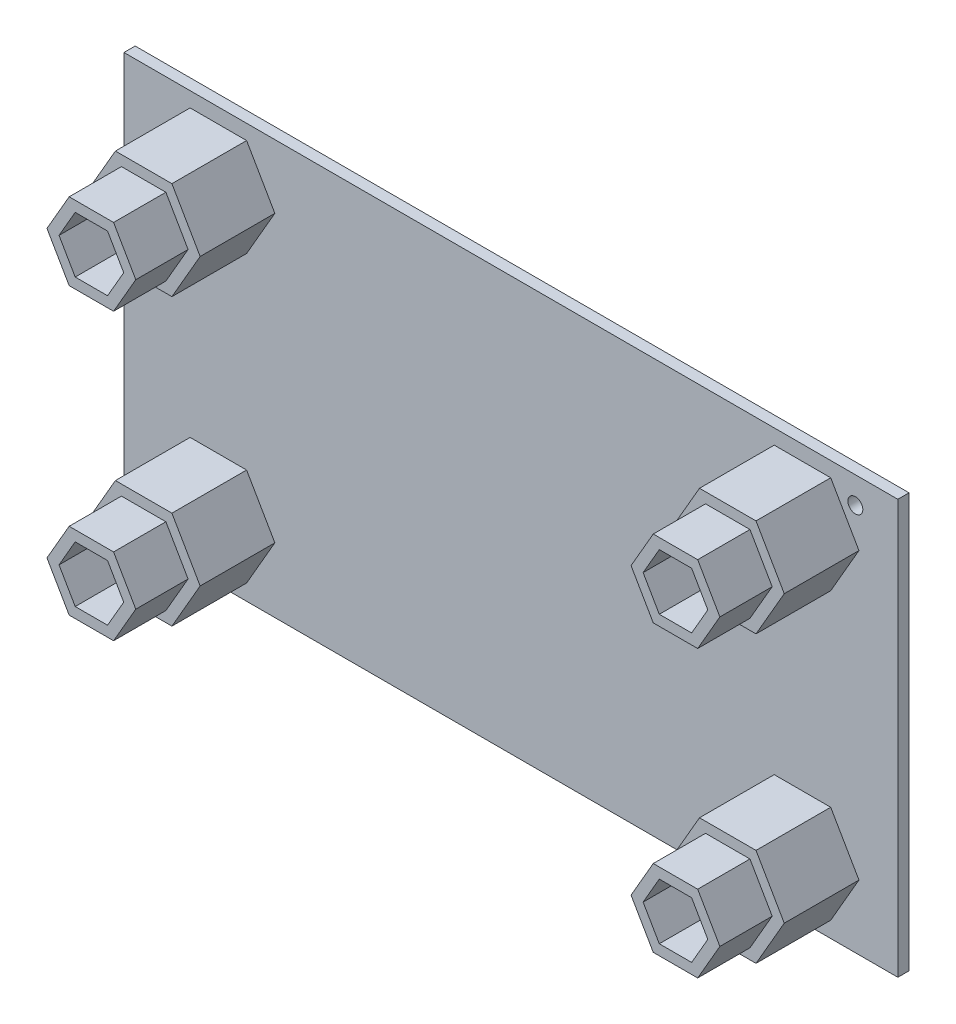
SolidWorks part; units mm, degrees
ref_plane "Front Plane" through (0, 0, 0) normal (0, 0, 1) x (1, 0, 0)
ref_plane "Top Plane" through (0, 0, 0) normal (0, 1, 0) x (1, 0, 0)
ref_plane "Right Plane" through (0, 0, 0) normal (1, 0, 0) x (0, 0, -1)
sketch "Sketch1" plane through (0, 0, 0) normal (0, 0, 1) x (1, 0, 0)
  line L1 (0, 0) -> (103.6, 0)
  line L2 (0, 0) -> (0, 55.42)
  line L3 (0, 55.42) -> (103.6, 55.42)
  line L4 (103.6, 0) -> (103.6, 55.42)
  dimension "D1" = 103.6
  dimension "D2" = 55.42
extrude "Boss-Extrude1" add sketch "Sketch1" along normal blind 1.5
sketch "Sketch2" plane through (0, 0, 0) normal (0, 0, -1) x (-1, 0, 0)
  line L0 (-103.6, 3.54) -> (0, 3.54) construction
  line L1 (-103.6, 0) -> (-103.6, 55.42) construction
  line L2 (0, 55.42) -> (0, 0) construction
  line L3 (0, 0) -> (-103.6, 0) construction
  line L4 (-103.6, 51.88) -> (0, 51.88) construction
  line L5 (-55.3364, 55.42) -> (-55.3364, 51.88) construction
  line L6 (-103.6, 55.42) -> (0, 55.42) construction
  line L7 (-47.0331, 0) -> (-47.0331, 3.54) construction
  circle A0 centre (-90.42, 3.54) radius 1
  circle A1 centre (-15.28, 3.54) radius 1
  circle A2 centre (-97.91, 51.88) radius 1
  circle A3 centre (-15.28, 51.88) radius 1
  dimension "D3" = 2
  dimension "D1" = 3.54
  dimension "D2" = 5.69
  dimension "D4" = 75.14
  dimension "D5" = 7.49
extrude "Cut-Extrude1" cut sketch "Sketch2" against normal blind 1.5
sketch "Sketch3" plane through (0, 0, 1.5) normal (0, 0, 1) x (1, 0, 0)
  line L0 (0, 52.02) -> (103.6, 52.02) construction
  line L1 (0, 55.42) -> (0, 0) construction
  line L2 (103.6, 0) -> (103.6, 55.42) construction
  line L3 (28.7266, 55.42) -> (28.7266, 52.02) construction
  line L4 (103.6, 55.42) -> (0, 55.42) construction
  line L5 (0, 27.77) -> (103.6, 27.77) construction
  line L6 (9.6634, 41.72) -> (15.6101, 41.72)
  line L7 (15.6101, 41.72) -> (18.5834, 46.87)
  line L8 (18.5834, 46.87) -> (15.6101, 52.02)
  line L9 (15.6101, 52.02) -> (9.6634, 52.02)
  line L10 (9.6634, 52.02) -> (6.69, 46.87)
  line L11 (6.69, 46.87) -> (9.6634, 41.72)
  line L12 (6.69, 8.67) -> (9.6634, 13.82)
  line L13 (9.6634, 3.52) -> (6.69, 8.67)
  line L14 (15.6101, 3.52) -> (9.6634, 3.52)
  line L15 (18.5834, 8.67) -> (15.6101, 3.52)
  line L16 (15.6101, 13.82) -> (18.5834, 8.67)
  line L17 (9.6634, 13.82) -> (15.6101, 13.82)
  line L18 (51.7334, -0.2211) -> (51.7334, 55.1859) construction
  line L20 (96.7768, 46.87) -> (93.8035, 41.72)
  line L21 (93.8035, 52.02) -> (96.7768, 46.87)
  line L22 (87.8568, 52.02) -> (93.8035, 52.02)
  line L23 (84.8834, 46.87) -> (87.8568, 52.02)
  line L24 (87.8568, 41.72) -> (84.8834, 46.87)
  line L25 (93.8035, 41.72) -> (87.8568, 41.72)
  line L26 (93.8035, 13.82) -> (87.8568, 13.82)
  line L27 (87.8568, 13.82) -> (84.8834, 8.67)
  line L28 (84.8834, 8.67) -> (87.8568, 3.52)
  line L29 (87.8568, 3.52) -> (93.8035, 3.52)
  line L30 (93.8035, 3.52) -> (96.7768, 8.67)
  line L31 (96.7768, 8.67) -> (93.8035, 13.82)
  circle A0 centre (12.6367, 46.87) radius 5.15 construction
  circle A1 centre (12.6367, 8.67) radius 5.15 construction
  circle A2 centre (90.8301, 46.87) radius 5.15 construction
  circle A3 centre (90.8301, 8.67) radius 5.15 construction
  dimension "D1" = 3.4
  dimension "D2" = 10.3
  dimension "D3" = 6.69
  dimension "D4" = 66.3
  dimension "D5" = 38.2
extrude "Boss-Extrude2" add sketch "Sketch3" along normal blind 17
sketch "Sketch4" plane through (0, 0, 1.5) normal (0, 0, 1) x (1, 0, 0)
  line L4 (18.5834, 46.87) -> (16.0554, 51.2486) construction
  line L5 (15.6101, 41.72) -> (18.5834, 46.87) construction
  line L6 (16.0554, 51.2486) -> (15.6101, 52.02) construction
  line L7 (15.6101, 52.02) -> (14.2898, 52.02) construction
  line L36 (14.2898, 52.02) -> (9.6634, 52.02) construction
  line L37 (9.6634, 52.02) -> (6.69, 46.87) construction
  line L38 (6.69, 46.87) -> (9.6634, 41.72) construction
  line L39 (9.6634, 41.72) -> (15.6101, 41.72) construction
  line L40 (9.6634, 3.52) -> (14.2802, 3.52) construction
  line L41 (15.6101, 3.52) -> (16.0138, 4.2193) construction
  line L42 (16.0138, 4.2193) -> (18.5834, 8.67) construction
  line L43 (14.2802, 3.52) -> (15.6101, 3.52) construction
  line L44 (18.5834, 8.67) -> (15.6101, 13.82) construction
  line L45 (15.6101, 13.82) -> (9.6634, 13.82) construction
  line L46 (9.6634, 13.82) -> (6.69, 8.67) construction
  line L47 (6.69, 8.67) -> (9.6634, 3.52) construction
  line L48 (84.8834, 8.67) -> (87.8568, 3.52) construction
  line L49 (87.8568, 13.82) -> (84.8834, 8.67) construction
  line L50 (91.4198, 3.52) -> (93.8035, 3.52) construction
  line L51 (89.4202, 3.52) -> (91.4198, 3.52) construction
  line L52 (87.8568, 3.52) -> (89.4202, 3.52) construction
  line L53 (93.8035, 3.52) -> (96.7768, 8.67) construction
  line L54 (96.7768, 8.67) -> (93.8035, 13.82) construction
  line L55 (93.8035, 13.82) -> (87.8568, 13.82) construction
  line L58 (96.7768, 46.87) -> (93.8035, 52.02) construction
  line L59 (93.8035, 52.02) -> (87.8568, 52.02) construction
  line L60 (93.8035, 41.72) -> (96.7768, 46.87) construction
  line L61 (87.8568, 41.72) -> (93.8035, 41.72) construction
  line L62 (84.8834, 46.87) -> (87.8568, 41.72) construction
  line L63 (87.8568, 52.02) -> (84.8834, 46.87) construction
  line L64 (18.5834, 46.87) -> (16.0554, 51.2486)
  line L65 (15.6101, 41.72) -> (18.5834, 46.87)
  line L66 (16.0554, 51.2486) -> (15.6101, 52.02)
  line L67 (15.6101, 52.02) -> (14.2898, 52.02)
  line L68 (14.2898, 52.02) -> (9.6634, 52.02)
  line L69 (9.6634, 52.02) -> (6.69, 46.87)
  line L70 (6.69, 46.87) -> (9.6634, 41.72)
  line L71 (9.6634, 41.72) -> (15.6101, 41.72)
  line L72 (9.6634, 3.52) -> (14.2802, 3.52)
  line L73 (15.6101, 3.52) -> (16.0138, 4.2193)
  line L74 (16.0138, 4.2193) -> (18.5834, 8.67)
  line L75 (14.2802, 3.52) -> (15.6101, 3.52)
  line L76 (18.5834, 8.67) -> (15.6101, 13.82)
  line L77 (15.6101, 13.82) -> (9.6634, 13.82)
  line L78 (9.6634, 13.82) -> (6.69, 8.67)
  line L79 (6.69, 8.67) -> (9.6634, 3.52)
  line L80 (84.8834, 8.67) -> (87.8568, 3.52)
  line L81 (87.8568, 13.82) -> (84.8834, 8.67)
  line L82 (91.4198, 3.52) -> (93.8035, 3.52)
  line L83 (89.4202, 3.52) -> (91.4198, 3.52)
  line L84 (87.8568, 3.52) -> (89.4202, 3.52)
  line L85 (93.8035, 3.52) -> (96.7768, 8.67)
  line L86 (96.7768, 8.67) -> (93.8035, 13.82)
  line L87 (93.8035, 13.82) -> (87.8568, 13.82)
  line L88 (96.7768, 46.87) -> (93.8035, 52.02)
  line L89 (93.8035, 52.02) -> (87.8568, 52.02)
  line L90 (93.8035, 41.72) -> (96.7768, 46.87)
  line L91 (87.8568, 41.72) -> (93.8035, 41.72)
  line L92 (84.8834, 46.87) -> (87.8568, 41.72)
  line L93 (87.8568, 52.02) -> (84.8834, 46.87)
  line L94 (20.2, 46.87) -> (17.2679, 51.9486)
  line L95 (17.2679, 51.9486) -> (16.4184, 53.42)
  line L96 (16.4184, 53.42) -> (14.2898, 53.42)
  line L97 (14.2898, 53.42) -> (8.8551, 53.42)
  line L98 (8.8551, 53.42) -> (5.0734, 46.87)
  line L99 (5.0734, 46.87) -> (8.8551, 40.32)
  line L100 (8.8551, 40.32) -> (16.4184, 40.32)
  line L101 (16.4184, 40.32) -> (20.2, 46.87)
  line L102 (8.8551, 2.12) -> (14.2802, 2.12)
  line L103 (14.2802, 2.12) -> (16.4184, 2.12)
  line L104 (16.4184, 2.12) -> (17.2263, 3.5193)
  line L105 (17.2263, 3.5193) -> (20.2, 8.67)
  line L106 (20.2, 8.67) -> (16.4184, 15.22)
  line L107 (16.4184, 15.22) -> (8.8551, 15.22)
  line L108 (8.8551, 15.22) -> (5.0734, 8.67)
  line L109 (5.0734, 8.67) -> (8.8551, 2.12)
  line L110 (83.2668, 8.67) -> (87.0485, 2.12)
  line L111 (87.0485, 2.12) -> (89.4202, 2.12)
  line L112 (89.4202, 2.12) -> (91.4198, 2.12)
  line L113 (91.4198, 2.12) -> (94.6118, 2.12)
  line L114 (94.6118, 2.12) -> (98.3934, 8.67)
  line L115 (98.3934, 8.67) -> (94.6118, 15.22)
  line L116 (94.6118, 15.22) -> (87.0485, 15.22)
  line L117 (87.0485, 15.22) -> (83.2668, 8.67)
  line L118 (98.3934, 46.87) -> (94.6118, 53.42)
  line L119 (94.6118, 53.42) -> (87.0485, 53.42)
  line L120 (87.0485, 53.42) -> (83.2668, 46.87)
  line L121 (83.2668, 46.87) -> (87.0485, 40.32)
  line L122 (87.0485, 40.32) -> (94.6118, 40.32)
  line L123 (94.6118, 40.32) -> (98.3934, 46.87)
  dimension "D1" = 1.4
extrude "Boss-Extrude4" add sketch "Sketch4" along normal blind 10
sketch "Sketch5" plane through (0, 0, 18.5) normal (0, 0, 1) x (1, 0, 0)
  line L0 (96.7768, 8.67) -> (93.8035, 13.82) construction
  line L1 (93.8035, 13.82) -> (87.8568, 13.82) construction
  line L2 (87.8568, 13.82) -> (84.8834, 8.67) construction
  line L3 (84.8834, 8.67) -> (87.8568, 3.52) construction
  line L4 (87.8568, 3.52) -> (93.8035, 3.52) construction
  line L5 (93.8035, 3.52) -> (96.7768, 8.67) construction
  line L6 (6.69, 46.87) -> (9.6634, 41.72) construction
  line L7 (9.6634, 41.72) -> (15.6101, 41.72) construction
  line L8 (15.6101, 41.72) -> (18.5834, 46.87) construction
  line L9 (18.5834, 46.87) -> (15.6101, 52.02) construction
  line L10 (15.6101, 52.02) -> (9.6634, 52.02) construction
  line L11 (9.6634, 52.02) -> (6.69, 46.87) construction
  line L12 (6.69, 8.67) -> (9.6634, 3.52) construction
  line L13 (9.6634, 3.52) -> (15.6101, 3.52) construction
  line L14 (15.6101, 3.52) -> (18.5834, 8.67) construction
  line L15 (18.5834, 8.67) -> (15.6101, 13.82) construction
  line L16 (15.6101, 13.82) -> (9.6634, 13.82) construction
  line L17 (9.6634, 13.82) -> (6.69, 8.67) construction
  line L18 (96.7768, 46.87) -> (93.8035, 52.02) construction
  line L19 (93.8035, 52.02) -> (87.8568, 52.02) construction
  line L20 (87.8568, 52.02) -> (84.8834, 46.87) construction
  line L21 (84.8834, 46.87) -> (87.8568, 41.72) construction
  line L22 (87.8568, 41.72) -> (93.8035, 41.72) construction
  line L23 (93.8035, 41.72) -> (96.7768, 46.87) construction
  line L24 (96.7768, 8.67) -> (93.8035, 13.82)
  line L25 (93.8035, 13.82) -> (87.8568, 13.82)
  line L26 (87.8568, 13.82) -> (84.8834, 8.67)
  line L27 (84.8834, 8.67) -> (87.8568, 3.52)
  line L28 (87.8568, 3.52) -> (93.8035, 3.52)
  line L29 (93.8035, 3.52) -> (96.7768, 8.67)
  line L30 (6.69, 46.87) -> (9.6634, 41.72)
  line L31 (9.6634, 41.72) -> (15.6101, 41.72)
  line L32 (15.6101, 41.72) -> (18.5834, 46.87)
  line L33 (18.5834, 46.87) -> (15.6101, 52.02)
  line L34 (15.6101, 52.02) -> (9.6634, 52.02)
  line L35 (9.6634, 52.02) -> (6.69, 46.87)
  line L36 (6.69, 8.67) -> (9.6634, 3.52)
  line L37 (9.6634, 3.52) -> (15.6101, 3.52)
  line L38 (15.6101, 3.52) -> (18.5834, 8.67)
  line L39 (18.5834, 8.67) -> (15.6101, 13.82)
  line L40 (15.6101, 13.82) -> (9.6634, 13.82)
  line L41 (9.6634, 13.82) -> (6.69, 8.67)
  line L42 (96.7768, 46.87) -> (93.8035, 52.02)
  line L43 (93.8035, 52.02) -> (87.8568, 52.02)
  line L44 (87.8568, 52.02) -> (84.8834, 46.87)
  line L45 (84.8834, 46.87) -> (87.8568, 41.72)
  line L46 (87.8568, 41.72) -> (93.8035, 41.72)
  line L47 (93.8035, 41.72) -> (96.7768, 46.87)
  line L48 (95.1603, 8.67) -> (92.9952, 12.42)
  line L49 (92.9952, 12.42) -> (88.6651, 12.42)
  line L50 (88.6651, 12.42) -> (86.5, 8.67)
  line L51 (86.5, 8.67) -> (88.6651, 4.92)
  line L52 (88.6651, 4.92) -> (92.9952, 4.92)
  line L53 (92.9952, 4.92) -> (95.1603, 8.67)
  line L54 (8.3066, 46.87) -> (10.4716, 43.12)
  line L55 (10.4716, 43.12) -> (14.8018, 43.12)
  line L56 (14.8018, 43.12) -> (16.9668, 46.87)
  line L57 (16.9668, 46.87) -> (14.8018, 50.62)
  line L58 (14.8018, 50.62) -> (10.4716, 50.62)
  line L59 (10.4716, 50.62) -> (8.3066, 46.87)
  line L60 (8.3066, 8.67) -> (10.4716, 4.92)
  line L61 (10.4716, 4.92) -> (14.8018, 4.92)
  line L62 (14.8018, 4.92) -> (16.9668, 8.67)
  line L63 (16.9668, 8.67) -> (14.8018, 12.42)
  line L64 (14.8018, 12.42) -> (10.4716, 12.42)
  line L65 (10.4716, 12.42) -> (8.3066, 8.67)
  line L66 (95.1603, 46.87) -> (92.9952, 50.62)
  line L67 (92.9952, 50.62) -> (88.6651, 50.62)
  line L68 (88.6651, 50.62) -> (86.5, 46.87)
  line L69 (86.5, 46.87) -> (88.6651, 43.12)
  line L70 (88.6651, 43.12) -> (92.9952, 43.12)
  line L71 (92.9952, 43.12) -> (95.1603, 46.87)
  dimension "D1" = 1.4
extrude "Cut-Extrude2" cut sketch "Sketch5" against normal blind 15 contours L58 L59 L54 L55 L56 L57 | L70 L71 L66 L67 L68 L69 | L52 L53 L48 L49 L50 L51 | L64 L65 L60 L61 L62 L63
